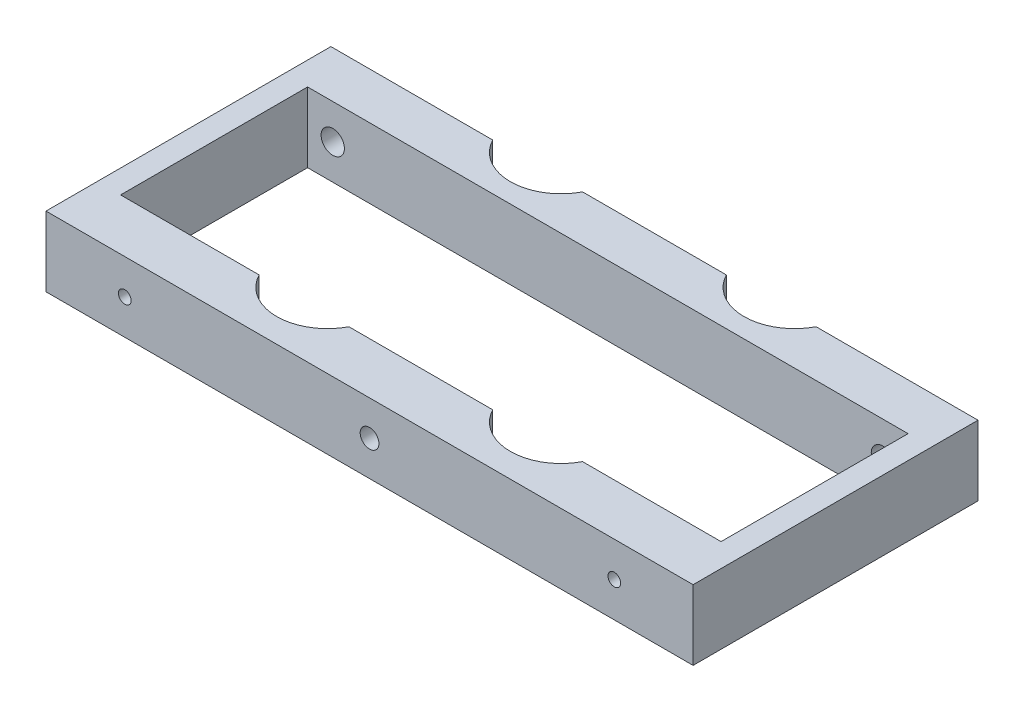
SolidWorks part; units mm, degrees
material "ABS"
ref_plane "Front Plane" through (0, 0, 0) normal (0, 0, 1) x (1, 0, 0)
ref_plane "Top Plane" through (0, 0, 0) normal (0, 1, 0) x (1, 0, 0)
ref_plane "Right Plane" through (0, 0, 0) normal (1, 0, 0) x (0, 0, -1)
sketch "Sketch1" plane through (0, 0, 0) normal (0, 1, 0) x (1, 0, 0)
  line L0 (68.5473, 77.6097) -> (107.7287, 77.6097)
  line L1 (0, 0) -> (176.276, 0)
  line L2 (0, 0) -> (0, 77.6097)
  line L3 (0, 77.6097) -> (44.089, 77.6097)
  line L4 (176.276, 0) -> (176.276, 77.6097)
  line L5 (132.187, 77.6097) -> (176.276, 77.6097)
  line L6 (132.187, 13.97) -> (169.926, 13.97)
  line L7 (169.926, 13.97) -> (169.926, 64.9097)
  line L9 (68.5473, 13.97) -> (107.7287, 13.97)
  line L10 (169.926, 64.9097) -> (6.35, 64.9097)
  line L11 (6.35, 64.9097) -> (6.35, 13.97)
  line L12 (6.35, 13.97) -> (44.089, 13.97)
  line L14 (56.3182, 83.9597) -> (119.9579, 83.9597) construction
  line L15 (56.3182, 20.32) -> (119.9579, 20.32) construction
  line L16 (56.3182, 83.9597) -> (56.3182, 20.32) construction
  circle A0 centre (56.3182, 83.9597) radius 13.7795
  circle A1 centre (119.9579, 83.9597) radius 13.7795
  arc A2 (44.089, 13.97) -> (68.5473, 13.97) centre (56.3182, 20.32) ccw
  arc A3 (107.7287, 13.97) -> (132.187, 13.97) centre (119.9579, 20.32) ccw
  dimension "D1" = 163.576
  dimension "D2" = 27.559
  dimension "D3" = 6.35
  dimension "D4" = 13.97
  dimension "D5" = 176.276
  dimension "D8" = 63.6397
  dimension "D6" = 6.35
  dimension "D7" = 6.35
  dimension "D9" = 12.7
extrude "Boss-Extrude1" add sketch "Sketch1" along normal blind 19.05 contours A1 L0 A0 L3 L2 L1 L4 L5 A3 L9 A2 L12 L11 L10 L7 L6
hole_wizard "#8-32 Tapped Hole1" positions "Sketch3" profile "Sketch2" tap size "#8-32" standard "ANSI Inch" end condition up to next
sketch "Sketch3" plane through (0, 0, 0) normal (0, 0, 1) x (1, 0, 0)
  line L3 (88.138, 19.05) -> (88.138, 0) construction
  line L5 (0, 19.05) -> (176.276, 19.05) construction
  line L6 (0, 0) -> (176.276, 0) construction
  line L7 (0, 9.525) -> (176.276, 9.525) construction
  line L8 (0, 19.05) -> (0, 0) construction
  line L9 (176.276, 19.05) -> (176.276, 0) construction
  point P0 (154.813, 9.525)
  point P18 (21.463, 9.525)
  dimension "D1" = 133.35
sketch "Sketch2" plane through (154.813, 9.525, 0) normal (1, 0, 0) x (0, -1, 0)
  line L0 (0, 0) -> (0, 13.97)
  line L1 (0, 13.97) -> (1.7272, 13.97)
  line L2 (1.7272, 13.97) -> (1.7272, 0)
  line L5 (1.7272, 0) -> (0, 0)
  line L11 (0, -6.35) -> (0, 107.95) construction
  dimension "Thru Tap Drill Dia." = 3.4544
  dimension "Thru Tap Drill Depth" = 13.97
cosmetic thread "Hole Thread3" parameters "D2"=4.1656
cosmetic thread "Hole Thread4" parameters "D2"=4.1656
hole_wizard "#10 Clearance Hole1" positions "Sketch5" profile "Sketch4" hole size "#10" standard "ANSI Inch" end condition up to next
sketch "Sketch5" plane through (0, 0, 0) normal (0, 0, 1) x (1, 0, 0)
  line L0 (0, 19.05) -> (176.276, 0) construction
  point P0 (88.138, 9.525)
sketch "Sketch4" plane through (88.138, 9.525, 0) normal (1, 0, 0) x (0, -1, 0)
  line L0 (0, 0) -> (0, 13.97)
  line L1 (0, 13.97) -> (2.5527, 13.97)
  line L2 (2.5527, 13.97) -> (2.5527, 0)
  line L5 (2.5527, 0) -> (0, 0)
  line L11 (0, -6.35) -> (0, 107.95) construction
  dimension "Thru Hole Dia." = 5.1054
  dimension "Thru Hole Depth" = 13.97
hole_wizard "1/4 (0.2500) Dowel Hole2" positions "Sketch9" profile "Sketch8" hole size "1/4" standard "ANSI Inch" end condition up to next
sketch "Sketch9" plane through (0, 0, -77.6097) normal (0, 0, -1) x (-1, 0, 0)
  circle A0 centre (-13.208, 9.525) radius 3.175 construction
  circle A1 centre (-163.068, 9.525) radius 3.175 construction
  point P0 (-13.208, 9.525)
  point P5 (-163.068, 9.525)
sketch "Sketch8" plane through (13.208, 9.525, -77.6097) normal (1, 0, 0) x (0, 1, 0)
  line L0 (0, 0) -> (0, 12.7)
  line L1 (0, 12.7) -> (3.175, 12.7)
  line L2 (3.175, 12.7) -> (3.175, 0)
  line L5 (3.175, 0) -> (0, 0)
  line L11 (0, -6.35) -> (0, 107.95) construction
  dimension "Thru Hole Dia." = 6.35
  dimension "Thru Hole Depth" = 12.7
